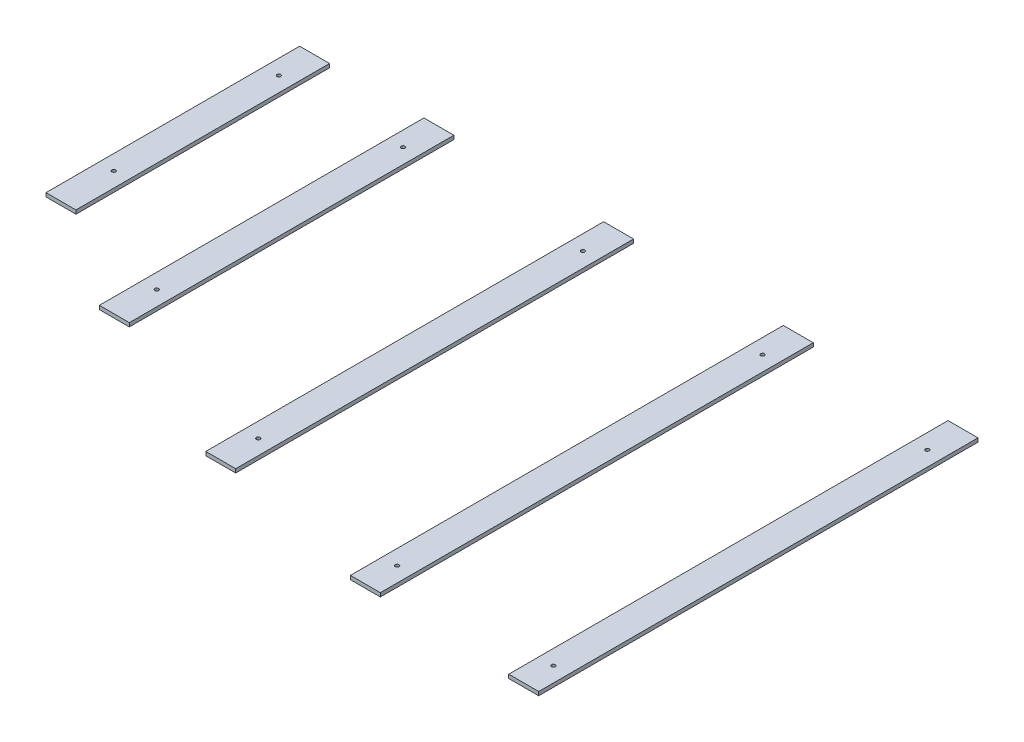
SolidWorks part; units mm, degrees
ref_plane "Front Plane" through (0, 0, 0) normal (0, 0, 1) x (1, 0, 0)
ref_plane "Top Plane" through (0, 0, 0) normal (0, 1, 0) x (1, 0, 0)
ref_plane "Right Plane" through (0, 0, 0) normal (1, 0, 0) x (0, 0, -1)
sketch "Sketch4" plane through (0, 0, 0) normal (0, 1, 0) x (1, 0, 0)
  line L4 (23232.9446, -10111.0305) -> (23232.9446, -10251.0305) construction
  line L5 (23232.9446, -9942.5829) -> (23032.9446, -9942.5829)
  line L6 (23232.9446, -9942.5829) -> (23232.9446, -12876.1567)
  line L7 (23232.9446, -12876.1567) -> (23032.9446, -12876.1567)
  line L8 (23032.9446, -9942.5829) -> (23032.9446, -12876.1567)
  line L9 (22132.9446, -9942.5829) -> (21932.9446, -9942.5829)
  line L10 (22132.9446, -9942.5829) -> (22132.9446, -12833.5838)
  line L11 (22132.9446, -12833.5838) -> (21932.9446, -12833.5838)
  line L12 (21932.9446, -9942.5829) -> (21932.9446, -12833.5838)
  line L13 (20932.9446, -9942.5829) -> (20732.9446, -9942.5829)
  line L14 (20932.9446, -9942.5829) -> (20932.9446, -12599.4325)
  line L15 (20932.9446, -12599.4325) -> (20732.9446, -12599.4325)
  line L16 (20732.9446, -9942.5829) -> (20732.9446, -12599.4325)
  line L17 (19732.9446, -9942.5829) -> (19532.9446, -9942.5829)
  line L18 (19732.9446, -9942.5829) -> (19732.9446, -12109.8436)
  line L19 (19732.9446, -12109.8436) -> (19532.9446, -12109.8436)
  line L20 (19532.9446, -9942.5829) -> (19532.9446, -12109.8436)
  line L21 (18902.9446, -9942.5829) -> (18702.9446, -9942.5829)
  line L22 (18902.9446, -9942.5829) -> (18902.9446, -11636.2195)
  line L23 (18902.9446, -11636.2195) -> (18702.9446, -11636.2195)
  line L24 (18702.9446, -9942.5829) -> (18702.9446, -11636.2195)
  line L25 (18702.9446, -10111.0305) -> (18702.9446, -10251.0305) construction
  line L26 (23132.9446, -12748.1199) -> (23132.9446, -12608.0593) construction
  line L27 (22032.9446, -12550.6075) -> (22032.9446, -12691.8491) construction
  line L28 (20832.9446, -12422.3488) -> (20832.9446, -12275.1597) construction
  line L29 (19632.9446, -11906.9658) -> (19632.9446, -11746.8651) construction
  line L30 (18802.9446, -11371.765) -> (18802.9446, -11195.5746) construction
  line L31 (23132.9446, -10251.0305) -> (23132.9446, -10111.0305) construction
  line L32 (18702.9446, -10251.0305) -> (23232.9446, -10251.0305) construction
  line L33 (23232.9446, -10111.0305) -> (18702.9446, -10111.0305) construction
  circle A0 centre (23132.9446, -12678.0896) radius 12.5
  arc A1 (18702.9446, -11295.1434) -> (23232.9446, -12744.4799) centre (22932.9446, -5878.0705) ccw construction
  arc A2 (18702.9446, -11116.3765) -> (23232.9446, -12604.3436) centre (22932.9446, -5878.0705) ccw construction
  circle A3 centre (22032.9446, -12621.2283) radius 12.5
  circle A4 centre (20832.9446, -12348.7542) radius 12.5
  circle A5 centre (19632.9446, -11826.9154) radius 12.5
  circle A6 centre (18802.9446, -11283.6698) radius 12.5
  circle A7 centre (18802.9446, -10181.0305) radius 12.5
  circle A8 centre (19632.9446, -10181.0305) radius 12.5
  circle A9 centre (20832.9446, -10181.0305) radius 12.5
  circle A10 centre (22032.9446, -10181.0305) radius 12.5
  circle A11 centre (23132.9446, -10181.0305) radius 12.5
  arc A12 (18702.9446, -11116.3765) -> (23232.9446, -12604.3436) centre (22932.9446, -5878.0705) ccw construction
  point P22 (23132.9446, -9942.5829)
  point P23 (22032.9446, -9942.5829)
  point P24 (20832.9446, -9942.5829)
  point P25 (19632.9446, -9942.5829)
  point P26 (23132.9446, -12876.1567)
  point P30 (20832.9446, -12599.4325)
  point P40 (23132.9446, -12678.0896)
  point P59 (22032.9446, -12621.2283)
  point P60 (22032.9446, -12833.5838)
  point P68 (20832.9446, -12348.7542)
  point P69 (19632.9446, -12109.8436)
  point P72 (0, 0)
  point P73 (19632.9446, -11826.9154)
  point P74 (18802.9446, -11283.6698)
  point P75 (18802.9446, -11636.2195)
  point P78 (23132.9446, -10181.0305)
  point P85 (0, 0)
  point P86 (0, 0)
  point P87 (23232.9446, -10227.7017)
  point P88 (0, 0)
  point P89 (0, 0)
  point P90 (0, 0)
  point P91 (18802.9446, -9942.5829)
  dimension "D5" = 25
  dimension "D1" = 200
  dimension "D2" = 1200
  dimension "D3" = 1200
  dimension "D4" = 1200
  dimension "D6" = 100
  dimension "D7" = 70
extrude "Boss-Extrude1" add sketch "Sketch4" along normal blind 25
